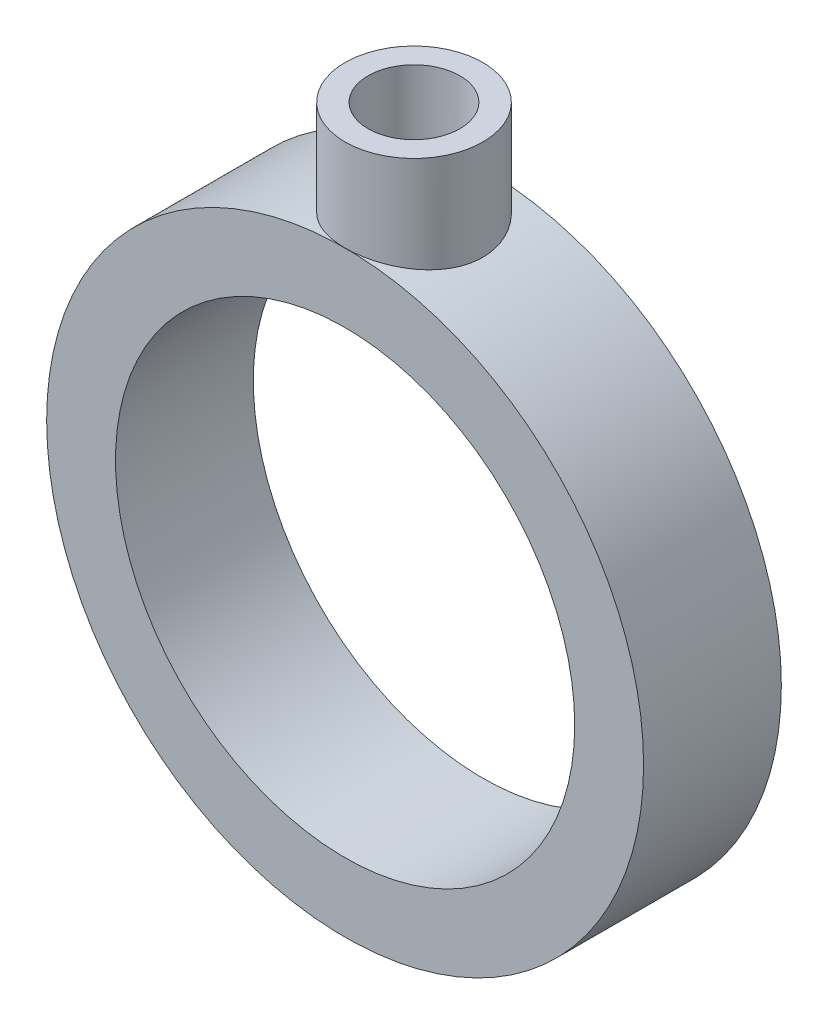
SolidWorks part; units mm, degrees
ref_plane "Front Plane" through (0, 0, 0) normal (0, 0, 1) x (1, 0, 0)
ref_plane "Top Plane" through (0, 0, 0) normal (0, 1, 0) x (1, 0, 0)
ref_plane "Right Plane" through (0, 0, 0) normal (1, 0, 0) x (0, 0, -1)
sketch "Sketch1" plane through (0, 0, 0) normal (0, 0, 1) x (1, 0, 0)
  circle A0 centre (0, 0) radius 10
  circle A1 centre (0, 0) radius 13
  dimension "D1" = 26
  dimension "D2" = 20
extrude "Boss-Extrude1" add sketch "Sketch1" along normal mid plane 6
sketch "Sketch2" plane through (0, 0, 0) normal (0, 1, 0) x (1, 0, 0)
  circle A0 centre (0, 0) radius 3
  dimension "D1" = 6
extrude "Boss-Extrude2" add sketch "Sketch2" against normal up to next from offset 17 separate body
sketch "Sketch3" plane through (0, 17, 0) normal (0, 1, 0) x (1, 0, 0)
  circle A0 centre (0, 0) radius 2
  dimension "D1" = 4
extrude "Cut-Extrude1" cut sketch "Sketch3" against normal blind 10
